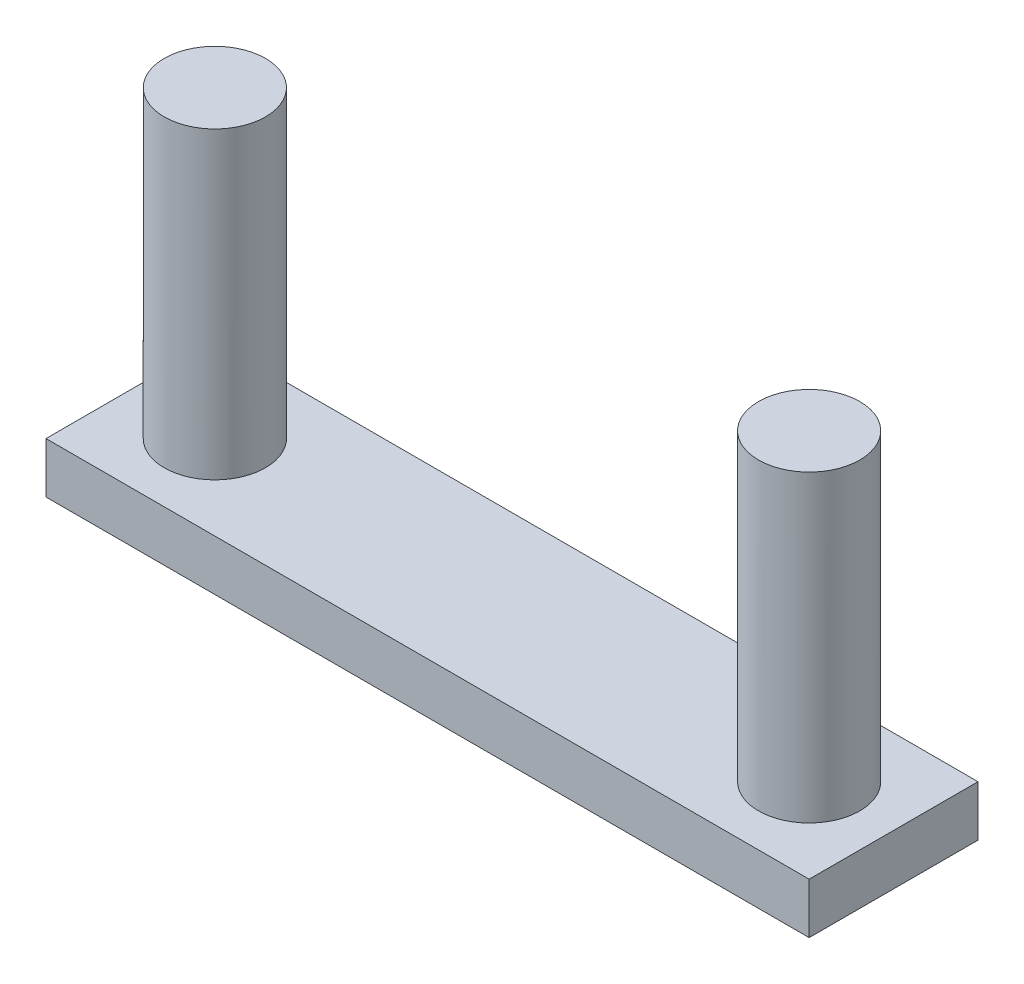
SolidWorks part; units mm, degrees
ref_plane "Front Plane" through (0, 0, 0) normal (0, 0, 1) x (1, 0, 0)
ref_plane "Top Plane" through (0, 0, 0) normal (0, 1, 0) x (1, 0, 0)
ref_plane "Right Plane" through (0, 0, 0) normal (1, 0, 0) x (0, 0, -1)
sketch "Sketch1" plane through (0, 0, 0) normal (0, 1, 0) x (1, 0, 0)
  line L1 (-78.4865, -37.3442) -> (-55.8865, -37.3442)
  line L2 (-78.4865, -37.3442) -> (-78.4865, -32.3442)
  line L3 (-78.4865, -32.3442) -> (-55.8865, -32.3442)
  line L4 (-55.8865, -37.3442) -> (-55.8865, -32.3442)
  dimension "D1" = 5
  dimension "D2" = 22.6
extrude "Boss-Extrude3" add sketch "Sketch1" along normal blind 1.5
sketch "Sketch3" plane through (0, 1.5, 0) normal (0, 1, 0) x (1, 0, 0)
  line L0 (-55.8865, -37.3442) -> (-55.8865, -32.3442) construction
  line L2 (-78.4865, -37.3442) -> (-55.8865, -37.3442) construction
  circle A0 centre (-75.9865, -34.8442) radius 1.5
  circle A1 centre (-58.3865, -34.8442) radius 1.5
  dimension "D1" = 3
  dimension "D2" = 3
  dimension "D3" = 17.6
  dimension "D4" = 2.5
  dimension "D5" = 2.5
  dimension "D6" = 2.5
extrude "Boss-Extrude4" add sketch "Sketch3" along normal blind 9
